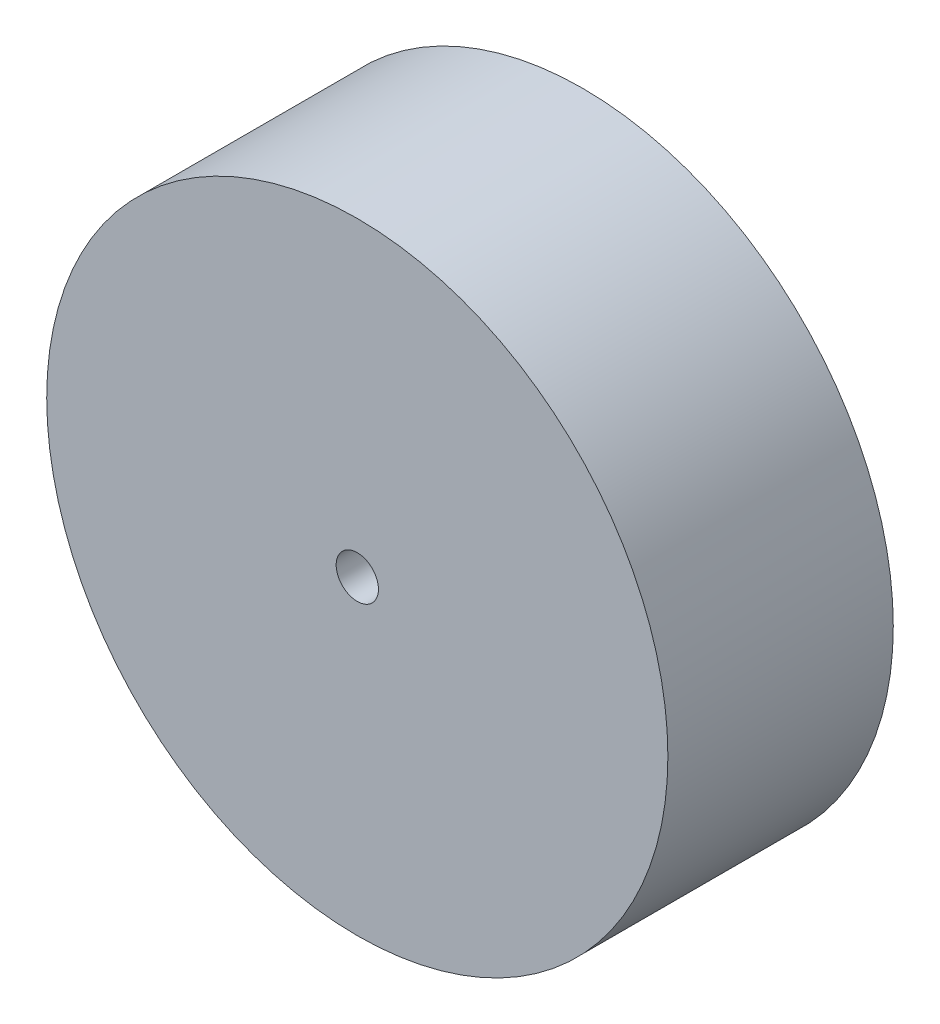
SolidWorks part; units mm, degrees
ref_plane "Front Plane" through (0, 0, 0) normal (0, 0, 1) x (1, 0, 0)
ref_plane "Top Plane" through (0, 0, 0) normal (0, 1, 0) x (1, 0, 0)
ref_plane "Right Plane" through (0, 0, 0) normal (1, 0, 0) x (0, 0, -1)
sketch "Sketch1" plane through (0, 0, 0) normal (0, 0, 1) x (1, 0, 0)
  circle A0 centre (0, 0) radius 35.0001
  circle A1 centre (0, 0) radius 2.3812
  dimension "D1" = 70.0001
  dimension "D2" = 4.7625
extrude "Boss-Extrude1" add sketch "Sketch1" along normal blind 25.4
